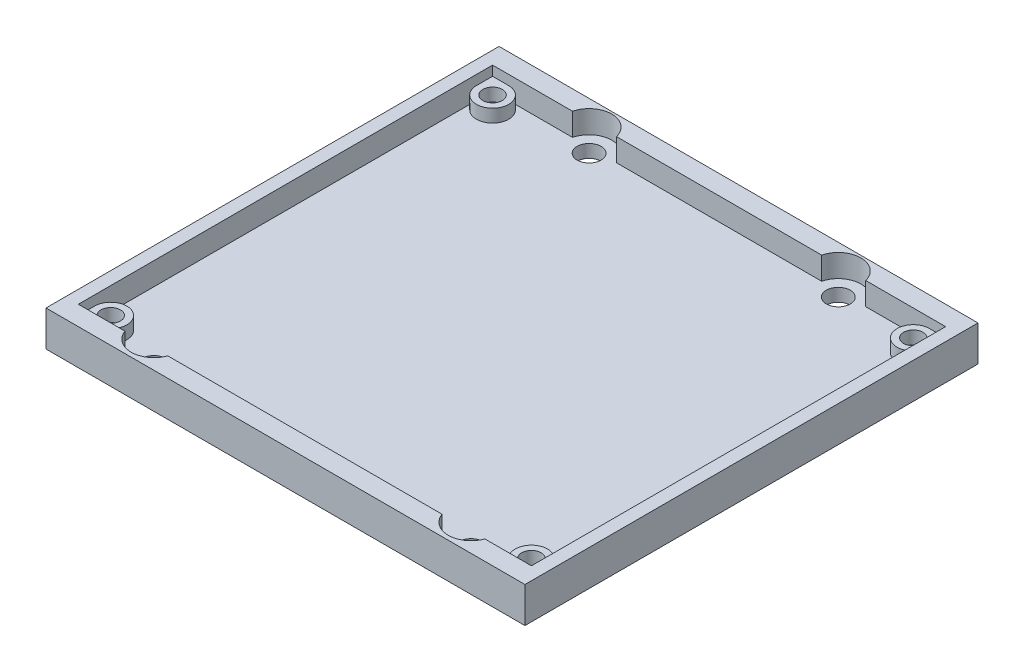
SolidWorks part; units mm, degrees
ref_plane "Front Plane" through (0, 0, 0) normal (0, 0, 1) x (1, 0, 0)
ref_plane "Top Plane" through (0, 0, 0) normal (0, 1, 0) x (1, 0, 0)
ref_plane "Right Plane" through (0, 0, 0) normal (1, 0, 0) x (0, 0, -1)
sketch "Sketch1" plane through (0, 0, 0) normal (0, 1, 0) x (1, 0, 0)
  line L0 (17.75, 66.1608) -> (37, 66.1608) construction
  line L7 (17.75, 66.1608) -> (12.5, 4.1608) construction
  line L8 (37, 66.1608) -> (37, 4.1608) construction
  line L9 (12.5, 4.1608) -> (37, 4.1608) construction
  line L10 (17.75, 66.1608) -> (17.75, 4.1608) construction
  line L11 (37, 35.1608) -> (0, 35) construction
  line L12 (0, 0) -> (74, 0)
  line L13 (0, 0) -> (0, 70)
  line L14 (0, 70) -> (17.2467, 70)
  line L15 (74, 0) -> (74, 70)
  line L16 (37, 35.1608) -> (74, 35) construction
  line L17 (18.2533, 70) -> (55.7467, 70)
  line L18 (56.7533, 70) -> (74, 70)
  line L19 (17.2467, 70) -> (18.2533, 70)
  line L20 (55.7467, 70) -> (56.7533, 70)
  circle A0 centre (17.75, 66.1608) radius 1.85
  circle A4 centre (12.5, 4.1608) radius 1.85
  circle A5 centre (61.5, 4.1608) radius 1.85
  circle A6 centre (56.25, 66.1608) radius 1.85
  dimension "D1" = 3.7
  dimension "D2" = 19.25
  dimension "D4" = 24.5
  dimension "D5" = 74
  dimension "D6" = 62
  dimension "70" = 70
extrude "Boss-Extrude1" add sketch "Sketch1" along normal blind 2
sketch "Sketch2" plane through (0, 2, 0) normal (0, 1, 0) x (1, 0, 0)
  line L0 (4.5, 5.5) -> (4.5, 0) construction
  line L1 (0, 0) -> (74, 0) construction
  line L2 (4.5, 64.5) -> (4.5, 70) construction
  line L3 (74, 70) -> (0, 70) construction
  line L4 (4.5, 5.5) -> (0, 5.5) construction
  line L5 (0, 70) -> (0, 0) construction
  line L6 (69.5, 5.5) -> (74, 5.5) construction
  line L7 (74, 0) -> (74, 70) construction
  line L8 (37, 70) -> (37, 0) construction
  line L9 (0, 70) -> (74, 70)
  line L10 (0, 70) -> (0, 0)
  line L11 (4.5, 3) -> (9.1981, 3)
  line L12 (2, 5.5) -> (2, 64.5)
  line L13 (4.5, 67) -> (14.3521, 67)
  line L14 (72, 5.5) -> (72, 64.5)
  line L15 (0, 0) -> (74, 0)
  line L16 (74, 70) -> (74, 0)
  line L17 (0, 35) -> (74, 35) construction
  line L18 (15.8019, 3) -> (58.1981, 3)
  line L19 (64.8019, 3) -> (69.5, 3)
  line L20 (17.75, 66.1608) -> (19.6, 66.1608) construction
  line L21 (21.1479, 67) -> (52.8521, 67)
  line L22 (59.6479, 67) -> (69.5, 67)
  circle A0 centre (4.5, 5.5) radius 1.5
  circle A1 centre (69.5, 5.5) radius 1.5
  circle A2 centre (69.5, 64.5) radius 1.5
  circle A3 centre (4.5, 64.5) radius 1.5
  arc A4 (4.5, 67) -> (2, 64.5) centre (4.5, 64.5) cw
  arc A5 (4.5, 3) -> (2, 5.5) centre (4.5, 5.5) ccw
  arc A6 (69.5, 3) -> (72, 5.5) centre (69.5, 5.5) cw
  arc A7 (69.5, 67) -> (72, 64.5) centre (69.5, 64.5) ccw
  arc A8 (9.1981, 3) -> (15.8019, 3) centre (12.5, 4.1608) ccw
  arc A9 (64.8019, 3) -> (58.1981, 3) centre (61.5, 4.1608) cw
  circle A10 centre (17.75, 66.1608) radius 1.85 construction
  arc A11 (21.1479, 67) -> (14.3521, 67) centre (17.75, 66.1608) ccw
  arc A12 (52.8521, 67) -> (59.6479, 67) centre (56.25, 66.1608) cw
  line M7 (0, 70) -> (0, 0)
  line M8 (0, 0) -> (74, 0)
  line M9 (74, 0) -> (74, 70)
  line M10 (74, 70) -> (0, 70)
  dimension "D1" = 64
  dimension "D8" = 1
  dimension "D6" = 3.5
  dimension "D7" = 3.5
  dimension "D3" = 3
  dimension "D2" = 70
  dimension "D4" = 2
  dimension "D5" = 2
extrude "Boss-Extrude2" add sketch "Sketch2" along normal blind 2 contours L14 L11 L12 L13 M10 M7 M8 M9
sketch "Sketch3" plane through (0, 4, 0) normal (0, 1, 0) x (1, 0, 0)
  line L0 (2, 64.5) -> (2, 67) construction
  line L1 (4.5, 67) -> (2, 67) construction
  line L2 (67.8282, 3) -> (72, 3) construction
  line L3 (72, 5.5) -> (72, 3) construction
  line L4 (9.1981, 3) -> (2, 3)
  line L5 (72, 3) -> (64.8019, 3)
  line L6 (72, 3) -> (72, 64.6)
  line L8 (2, 3) -> (2, 67)
  line L9 (0, 70) -> (74, 70)
  line L10 (0, 70) -> (0, 0)
  line L11 (0, 0) -> (74, 0)
  line L12 (74, 70) -> (74, 0)
  line L13 (58.1981, 3) -> (15.8019, 3)
  line L14 (4.5, 67) -> (2, 67)
  line L16 (4.5, 67) -> (14.3521, 67)
  line L17 (72, 67) -> (72, 64.6)
  line L18 (21.1479, 67) -> (52.8521, 67)
  line L20 (59.6479, 67) -> (72, 67)
  arc A0 (9.1981, 3) -> (15.8019, 3) centre (12.5, 4.1608) ccw
  arc A1 (9.1981, 3) -> (15.8019, 3) centre (12.5, 4.1608) ccw construction
  arc A4 (14.3521, 67) -> (21.1479, 67) centre (17.75, 66.1608) cw
  arc A6 (59.6479, 67) -> (52.8521, 67) centre (56.25, 66.1608) ccw
  arc A7 (58.1981, 3) -> (64.8019, 3) centre (61.5, 4.1608) ccw
extrude "Boss-Extrude3" add sketch "Sketch3" along normal blind 1.5
